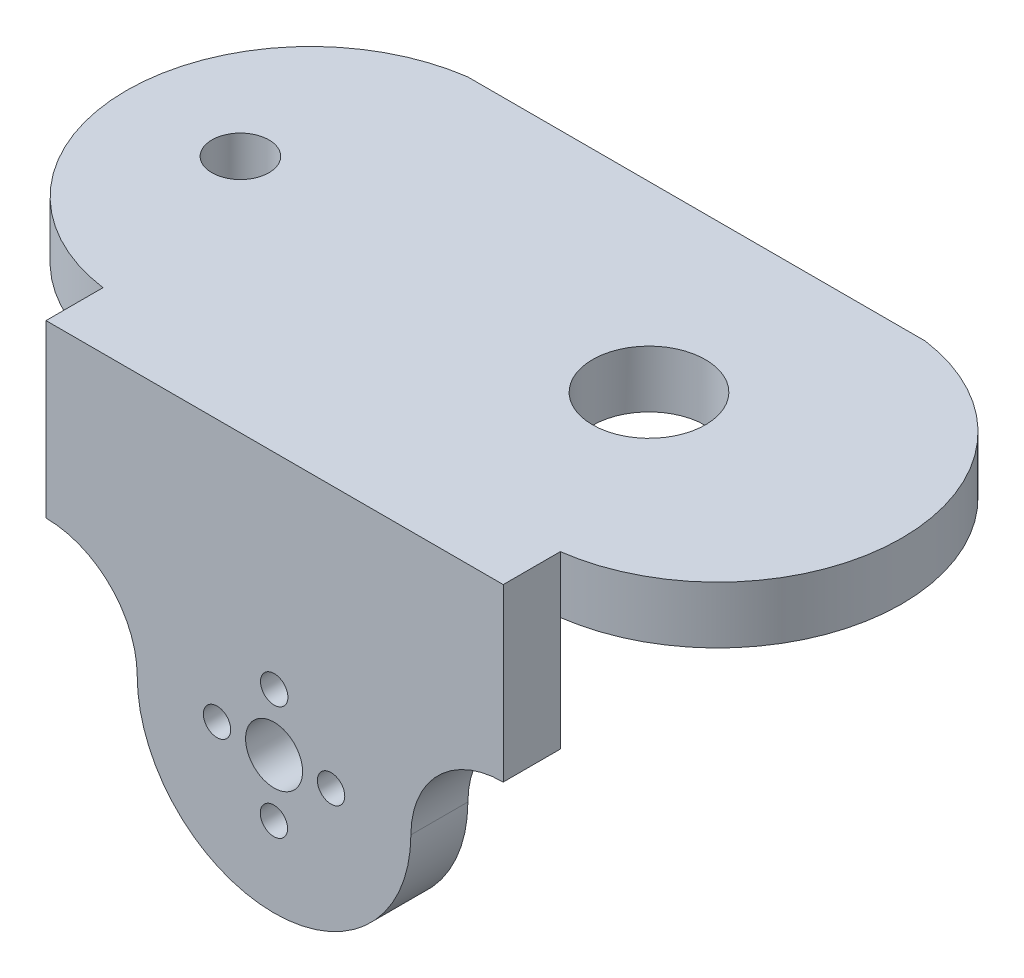
SolidWorks part; units mm, degrees
material "1060 Alloy"
ref_plane "Front" through (0, 0, 0) normal (0, 0, 1) x (1, 0, 0)
ref_plane "Top" through (0, 0, 0) normal (0, 1, 0) x (1, 0, 0)
ref_plane "Right" through (0, 0, 0) normal (1, 0, 0) x (0, 0, -1)
sketch "Sketch1" plane through (0, 0, 0) normal (0, 0, 1) x (1, 0, 0)
  line L1 (0, 0) -> (40.1, 0)
  line L2 (0, 0) -> (0, -10)
  line L3 (0, -10) -> (40.1, -10)
  line L4 (40.1, 0) -> (40.1, -10)
  arc A0 (0, -10) -> (8, -18) centre (0, -18) cw
  arc A1 (8, -18) -> (31.9999, -18.0599) centre (20, -18) ccw
  arc A2 (31.9999, -18.0599) -> (40.1, -10) centre (40.1, -18.1003) cw
  dimension "D3" = 8
  dimension "D4" = 12
  dimension "D1" = 40.1
  dimension "D2" = 10
extrude "Boss-Extrude1" add sketch "Sketch1" along normal blind 5 contours L4 L1 L2 L3 | A1 A2 L3 A0
sketch "Sketch2" plane through (0, 0, 5) normal (0, 0, 1) x (1, 0, 0)
  line L0 (40.1, 0) -> (40.1, -10) construction
  line L1 (0, 0) -> (40.1, 0)
  line L2 (0, 0) -> (0, 5)
  line L3 (0, 5) -> (40.1, 5)
  line L4 (40.1, 0) -> (40.1, 5)
  dimension "D1" = 5
extrude "Boss-Extrude2" add sketch "Sketch2" against normal blind 37
sketch "Sketch3" plane through (0, 5, 0) normal (0, 1, 0) x (1, 0, 0)
  line L0 (0, 32) -> (0, 0) construction
  line L1 (0, 32) -> (0, 0)
  line L4 (20.05, 32) -> (20.05, -5) construction
  line L5 (40.1, 32) -> (0, 32) construction
  line L6 (40.1, -5) -> (0, -5) construction
  line L7 (40.1, 32) -> (40.1, 0)
  arc A0 (0, 0) -> (0, 32) centre (2.2006, 16) cw
  arc A2 (40.1, 0) -> (40.1, 32) centre (37.8994, 16) ccw
  point P9 (-13.95, 16)
  dimension "D1" = 34
extrude "Boss-Extrude3" add sketch "Sketch3" against normal up to surface (5 mm away) up to face at (20.05, 0, -16)
sketch "Sketch4" plane through (0, 0, 5) normal (0, 0, 1) x (1, 0, 0)
  line L0 (20.0299, -6) -> (19.9701, -30) construction
  line L1 (8.0001, -17.9401) -> (31.9999, -18.0599) construction
  arc A0 (8, -18) -> (31.9999, -18.0599) centre (20, -18) ccw construction
  arc A1 (8, -18) -> (31.9999, -18.0599) centre (20, -18) ccw
  circle A2 centre (20, -18) radius 2.5
  circle A3 centre (20.0125, -13) radius 1.2
  circle A4 centre (15, -17.9751) radius 1.2
  circle A5 centre (19.9875, -23) radius 1.2
  circle A6 centre (25, -18.0249) radius 1.2
  point P7 (20, -18)
  point P10 (20, -18)
  dimension "D1" = 5
  dimension "D2" = 2.4
  dimension "D3" = 5
  dimension "D4" = 5
  dimension "D5" = 5
  dimension "D6" = 5
extrude "Cut-Extrude1" cut sketch "Sketch4" against normal through all contours A3 | A2 | A4 | A5 | A6
sketch "Sketch5" plane through (0, 5, 0) normal (0, 1, 0) x (1, 0, 0)
  line L0 (-13.95, 16) -> (54.05, 16) construction
  arc A0 (40.1, 0) -> (40.1, 32) centre (37.8994, 16) ccw construction
  arc A1 (0, 32) -> (0, 0) centre (2.2006, 16) ccw construction
  arc A2 (40.1, 0) -> (40.1, 32) centre (37.8994, 16) ccw
  arc A3 (0, 32) -> (0, 0) centre (2.2006, 16) ccw
  circle A4 centre (31.88, 16) radius 4.955
  circle A7 centre (-3.95, 16) radius 2.5
  dimension "D2" = 9.91
  dimension "D3" = 35.83
  dimension "D1" = 5
  dimension "D4" = 10
extrude "Cut-Extrude2" cut sketch "Sketch5" against normal through all
